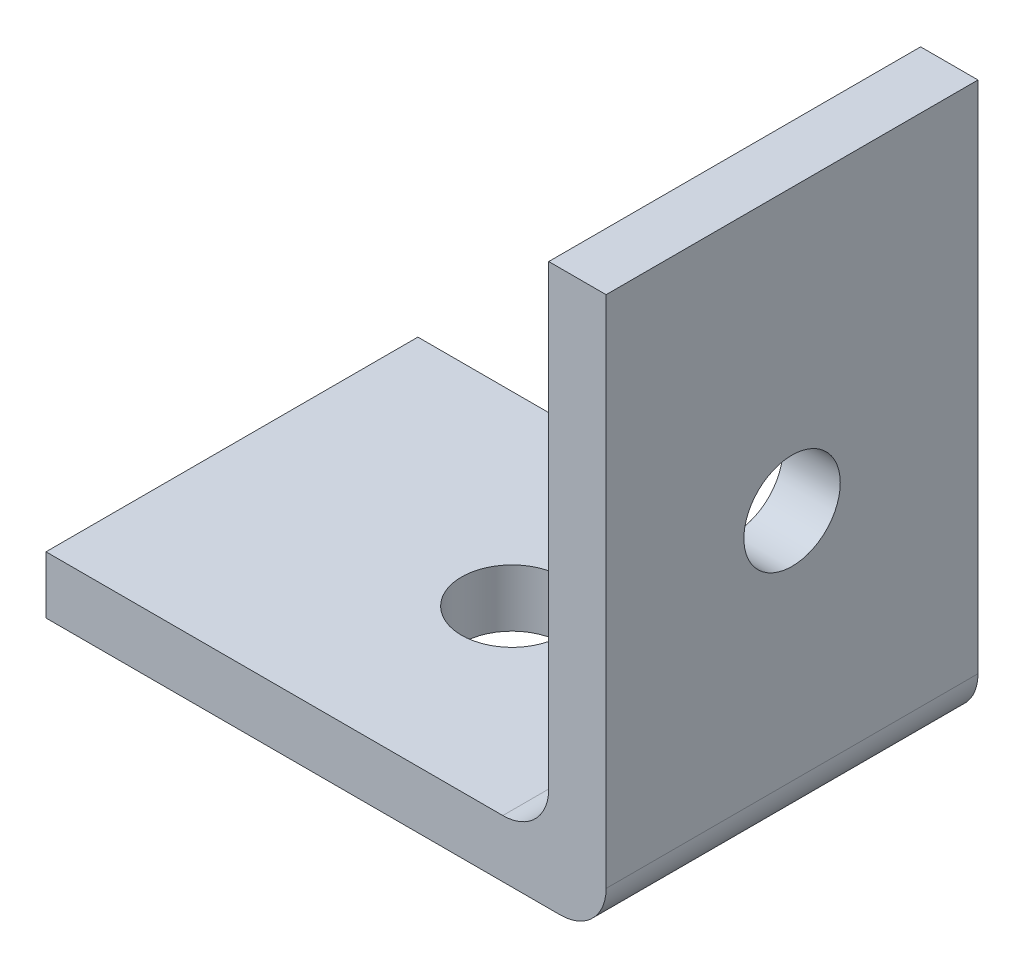
SolidWorks part; units mm, degrees
material "1060 Alloy"
ref_plane "Front Plane" through (0, 0, 0) normal (0, 0, 1) x (1, 0, 0)
ref_plane "Top Plane" through (0, 0, 0) normal (0, 1, 0) x (1, 0, 0)
ref_plane "Right Plane" through (0, 0, 0) normal (1, 0, 0) x (0, 0, -1)
sketch "Sketch1" plane through (0, 0, 0) normal (0, 0, 1) x (1, 0, 0)
  line L0 (12.319, 1.5875) -> (12.319, 29.4005)
  line L1 (12.319, 1.5875) -> (-15.494, 1.5875)
  line L4 (-15.494, 1.5875) -> (-15.494, -1.5875)
  line L5 (15.494, -1.5875) -> (-15.494, -1.5875)
  line L8 (15.494, -1.5875) -> (15.494, 29.4005)
  line L9 (15.494, 29.4005) -> (12.319, 29.4005)
  point P0 (0, 0)
  dimension "D2" = 3.175
  dimension "D4" = 3.175
extrude "Boss-Extrude1" add sketch "Sketch1" along normal blind 20.574
fillet "Fillet1" radius 2.54 1 edges at (12.319, 1.5875, 10.287)
fillet "Fillet2" radius 2.54 1 edges at (15.494, -1.5875, 10.287)
sketch "Sketch2" plane through (15.494, 0, 0) normal (1, 0, 0) x (0, 0, -1)
  line L0 (-20.574, 29.4005) -> (0, 29.4005) construction
  line L2 (-20.574, 0.9525) -> (-20.574, 29.4005) construction
  circle A0 centre (-10.287, 13.9065) radius 2.667
  dimension "D1" = 5.334
  dimension "D2" = 15.494
  dimension "D3" = 10.287
extrude "Cut-Extrude1" cut sketch "Sketch2" against normal through all
sketch "Sketch3" plane through (0, -1.5875, 0) normal (0, -1, 0) x (1, 0, 0)
  line L0 (-15.494, 20.574) -> (-15.494, 0) construction
  line L1 (-15.494, 20.574) -> (12.954, 20.574) construction
  circle A0 centre (0, 10.287) radius 2.794
  dimension "D1" = 5.588
  dimension "D2" = 15.494
  dimension "D3" = 10.287
extrude "Cut-Extrude2" cut sketch "Sketch3" against normal through all
